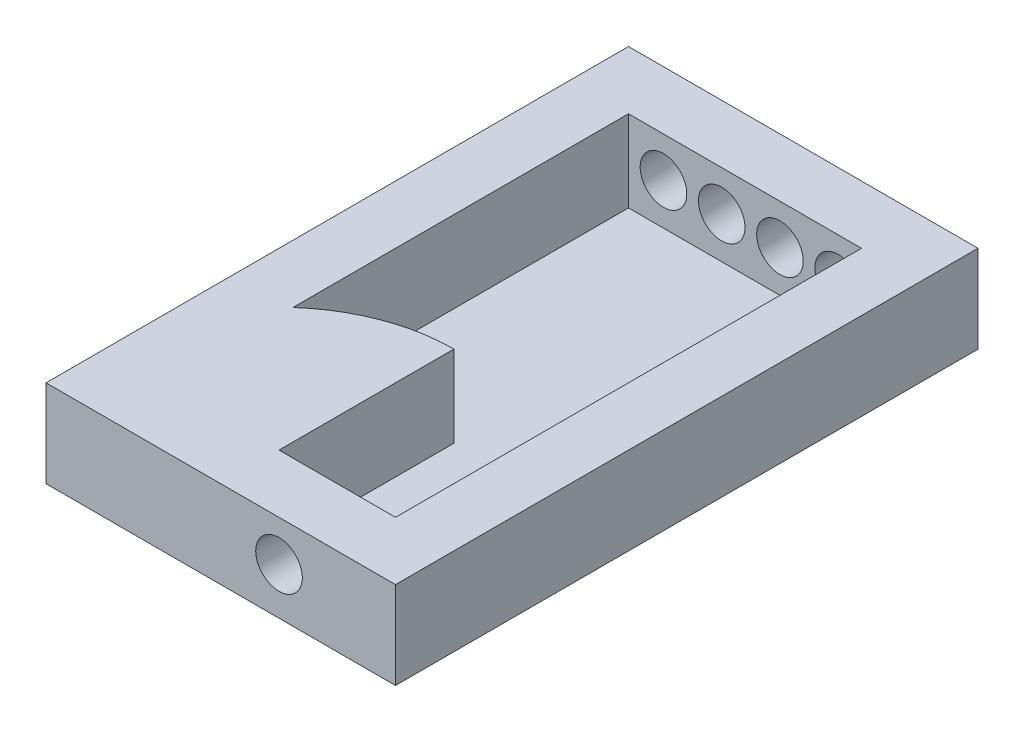
SolidWorks part; units mm, degrees
ref_plane "Alzado" through (0, 0, 0) normal (0, 0, 1) x (1, 0, 0)
ref_plane "Planta" through (0, 0, 0) normal (0, 1, 0) x (1, 0, 0)
ref_plane "Vista lateral" through (0, 0, 0) normal (1, 0, 0) x (0, 0, -1)
sketch "Croquis1" plane through (0, 0, 0) normal (0, 1, 0) x (1, 0, 0)
  line L1 (0, 0) -> (-60, 0)
  line L2 (0, 0) -> (0, 100)
  line L3 (0, 100) -> (-60, 100)
  line L4 (-60, 0) -> (-60, 100)
  dimension "D1" = 60
  dimension "D2" = 100
extrude "Saliente-Extruir3" add sketch "Croquis1" along normal blind 15
sketch "Croquis2" plane through (0, 15, 0) normal (0, 1, 0) x (1, 0, 0)
  line L0 (-60, 100) -> (-60, 0) construction
  line L1 (-10, 10) -> (-50, 10)
  line L2 (-10, 10) -> (-10, 90)
  line L3 (-10, 90) -> (-50, 90)
  line L4 (-50, 10) -> (-50, 90)
  line L5 (-60, 0) -> (0, 0) construction
  dimension "D1" = 40
  dimension "D2" = 80
  dimension "D3" = 10
  dimension "D4" = 10
extrude "Cortar-Extruir1" cut sketch "Croquis2" against normal blind 14
sketch "Croquis3" plane through (0, 1, 0) normal (0, 1, 0) x (1, 0, 0)
  line L0 (-50, 10) -> (-30, 10)
  line L1 (-50, 10) -> (-10, 10) construction
  line L2 (-30, 10) -> (-30, 40.0288)
  line L3 (-50, 90) -> (-50, 10) construction
  line L4 (-50, 32.3994) -> (-50, 10)
  arc A0 (-30, 40.0288) -> (-50, 32.3994) centre (-30, 10) ccw
extrude "Saliente-Extruir4" add sketch "Croquis3" along normal blind 14
sketch "Croquis4" plane through (0, 0, -100) normal (0, 0, -1) x (-1, 0, 0)
  line L1 (0, 15) -> (0, 0) construction
  circle A0 centre (14, 8.0935) radius 4
  circle A1 centre (24, 8.0935) radius 4
  circle A2 centre (34, 8.0935) radius 4
  circle A3 centre (44, 8.0935) radius 4
  dimension "D1" = 8
  dimension "D2" = 4
  dimension "D3" = 14
extrude "Cortar-Extruir2" cut sketch "Croquis4" against normal up to vertex (10 mm away)
sketch "Croquis5" plane through (0, 0, -10) normal (0, 0, -1) x (-1, 0, 0)
  line L0 (30, 15) -> (10, 15) construction
  line L1 (30, 15) -> (30, 1) construction
  circle A0 centre (20, 8) radius 4
  point P4 (0, 0)
  dimension "D1" = 8
  dimension "D2" = 7
  dimension "D3" = 10
extrude "Cortar-Extruir3" cut sketch "Croquis5" against normal blind 11
sketch "Croquis6" plane through (-30, 0, 0) normal (1, 0, 0) x (0, 0, -1)
  line L1 (40.0288, 15) -> (40.0288, 1) construction
  line L2 (10, 15) -> (40.0288, 15) construction
  circle A0 centre (24.8788, 8) radius 5
  dimension "D1" = 10
  dimension "D2" = 15.15
  dimension "D3" = 7
sketch "Croquis7" plane through (-60, 0, 0) normal (-1, 0, 0) x (0, 0, 1)
  circle A0 centre (-22.9722, 7.8955) radius 5
extrude "Cortar-Extruir5" cut sketch "Croquis7" against normal blind 28
